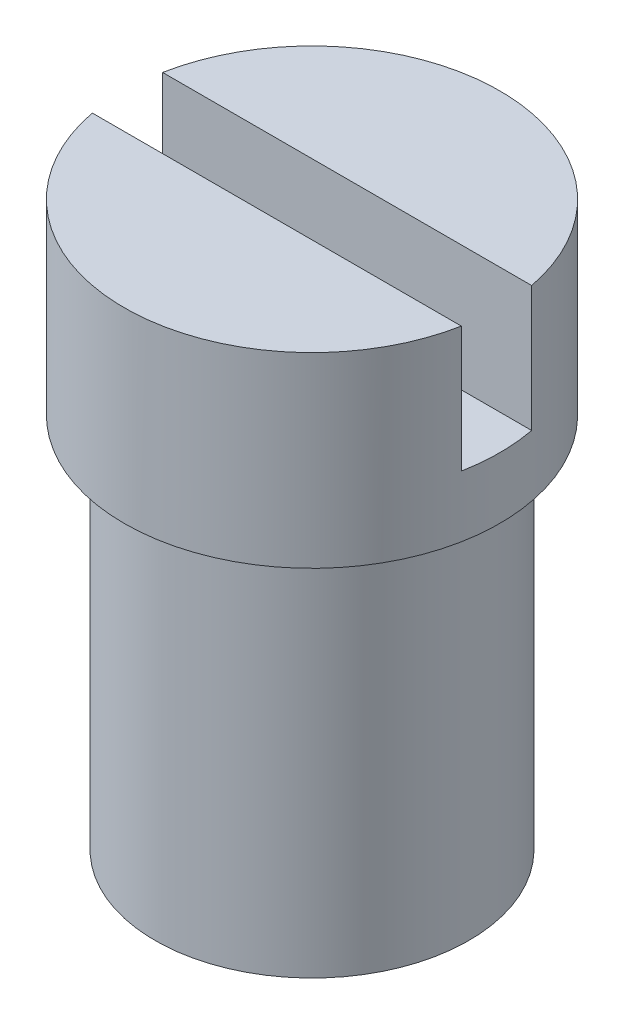
SolidWorks part; units mm, degrees
material "Brass"
ref_plane "Front Plane" through (0, 0, 0) normal (0, 0, 1) x (1, 0, 0)
ref_plane "Top Plane" through (0, 0, 0) normal (0, 1, 0) x (1, 0, 0)
ref_plane "Right Plane" through (0, 0, 0) normal (1, 0, 0) x (0, 0, -1)
sketch "Sketch1" plane through (0, 0, 0) normal (0, 1, 0) x (1, 0, 0)
  circle A0 centre (0, 0) radius 2.3749
  dimension "D1" = 4.7498
extrude "Boss-Extrude1" add sketch "Sketch1" along normal blind 2.3622
sketch "Sketch2" plane through (0, 0, 0) normal (0, -1, 0) x (-1, 0, 0)
  circle A0 centre (0, 0) radius 1.9844
  dimension "D1" = 3.9688
extrude "Boss-Extrude2" add sketch "Sketch2" along normal blind 4.7625
sketch "Sketch3" plane through (0, 2.3622, 0) normal (0, 1, 0) x (1, 0, 0)
  line L1 (-2.3749, -0.4445) -> (2.3749, -0.4445)
  line L2 (-2.3749, -0.4445) -> (-2.3749, 0.4445)
  line L3 (-2.3749, 0.4445) -> (2.3749, 0.4445)
  line L4 (2.3749, -0.4445) -> (2.3749, 0.4445)
  line L5 (-2.3749, -0.4445) -> (2.3749, 0.4445) construction
  line L6 (-2.3749, 0.4445) -> (2.3749, -0.4445) construction
  circle A0 centre (0, 0) radius 2.3749 construction
  point P0 (0, 0)
  dimension "D1" = 0.889
extrude "Cut-Extrude1" cut sketch "Sketch3" against normal blind 1.5875
